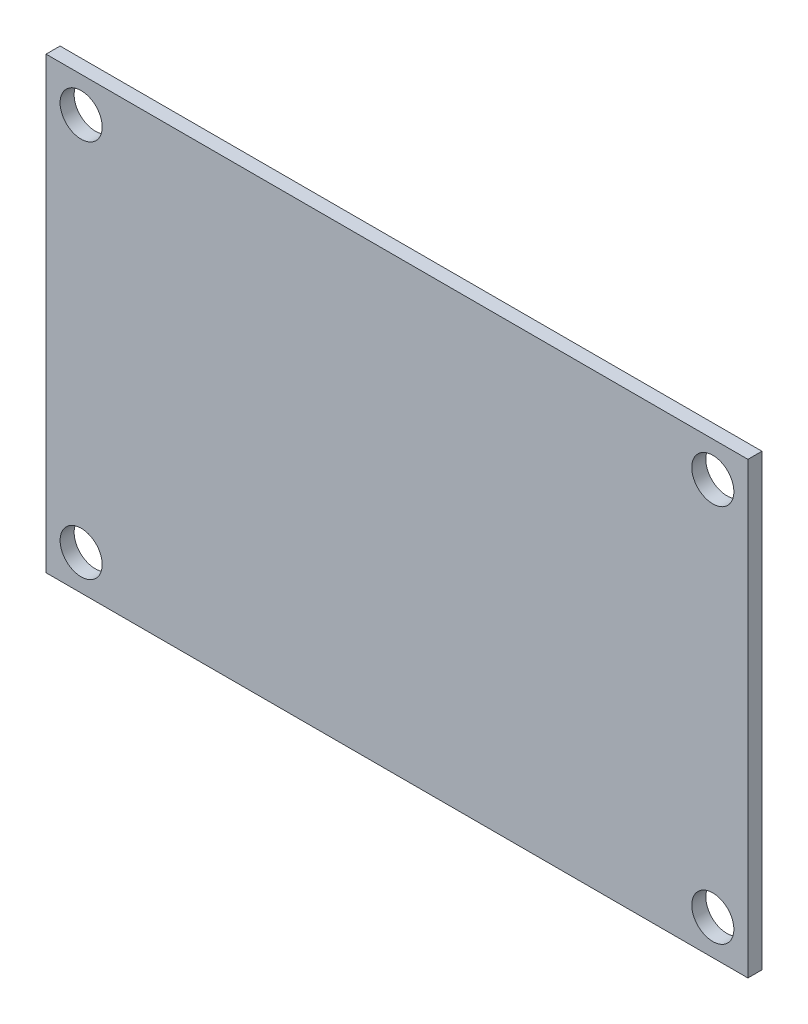
SolidWorks part; units mm, degrees
ref_plane "Plan de face" through (0, 0, 0) normal (0, 0, 1) x (1, 0, 0)
ref_plane "Plan de dessus" through (0, 0, 0) normal (0, 1, 0) x (1, 0, 0)
ref_plane "Plan de droite" through (0, 0, 0) normal (1, 0, 0) x (0, 0, -1)
sketch "Esquisse1" plane through (0, 0, 0) normal (0, 0, 1) x (1, 0, 0)
  line L1 (0, 0) -> (50, 0)
  line L2 (0, 0) -> (0, 32)
  line L3 (0, 32) -> (50, 32)
  line L4 (50, 0) -> (50, 32)
  dimension "D1" = 32
  dimension "D2" = 50
extrude "Boss.-Extru.1" add sketch "Esquisse1" along normal blind 1
sketch "Esquisse2" plane through (0, 0, 0) normal (0, 0, -1) x (-1, 0, 0)
  line L0 (-50, 32) -> (0, 32) construction
  line L1 (0, 32) -> (0, 0) construction
  line L2 (0, 16) -> (-50, 16) construction
  line L3 (-50, 0) -> (-50, 32) construction
  line L4 (-25, 32) -> (-25, 0) construction
  line L5 (0, 0) -> (-50, 0) construction
  circle A0 centre (-2.5, 29.5) radius 1.5
  circle A1 centre (-2.5, 2.5) radius 1.5
  circle A2 centre (-47.5, 2.5) radius 1.5
  circle A3 centre (-47.5, 29.5) radius 1.5
  dimension "D1" = 3
  dimension "D2" = 2.5
  dimension "D3" = 2.5
extrude "Enlèv. mat.-Extru.1" cut sketch "Esquisse2" against normal through all
